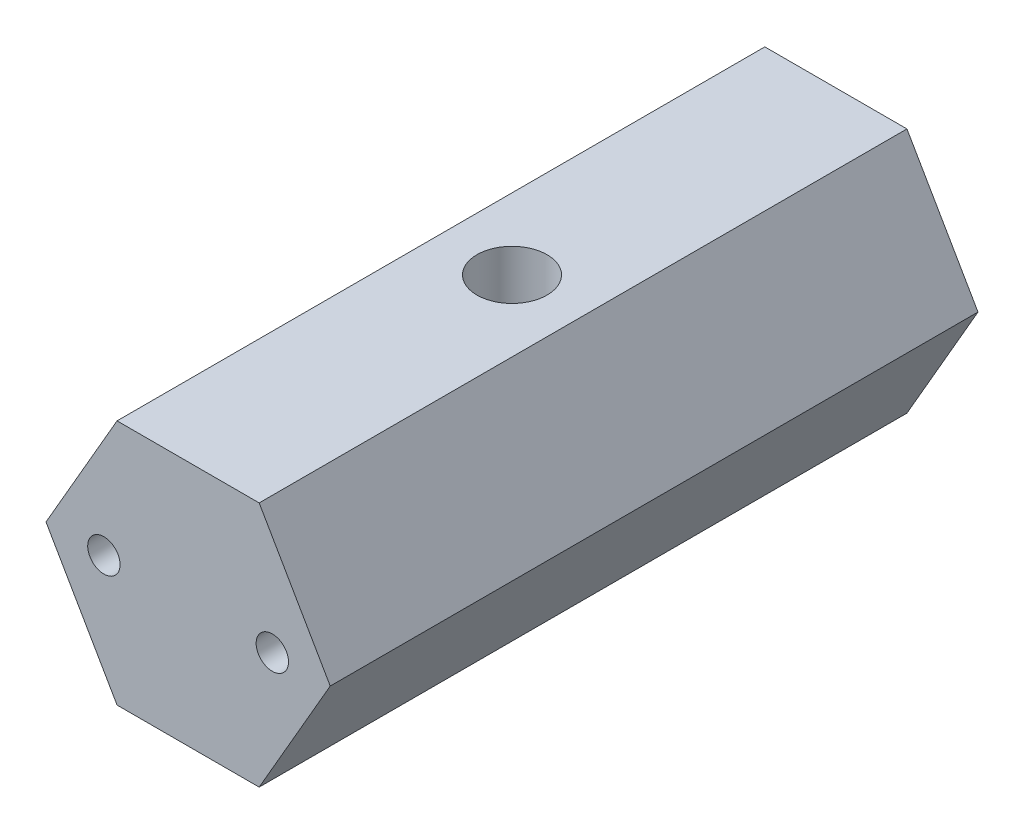
SolidWorks part; units mm, degrees
material "6061-T6 (SS)"
ref_plane "Front Plane" through (0, 0, 0) normal (0, 0, 1) x (1, 0, 0)
ref_plane "Top Plane" through (0, 0, 0) normal (0, 1, 0) x (1, 0, 0)
ref_plane "Right Plane" through (0, 0, 0) normal (1, 0, 0) x (0, 0, -1)
sketch "Sketch1" plane through (0, 0, 0) normal (0, 0, 1) x (1, 0, 0)
  line L1 (-5.4848, -9.5) -> (5.4848, -9.5)
  line L2 (5.4848, -9.5) -> (10.9697, 0)
  line L3 (10.9697, 0) -> (5.4848, 9.5)
  line L4 (5.4848, 9.5) -> (-5.4848, 9.5)
  line L5 (-5.4848, 9.5) -> (-10.9697, 0)
  line L6 (-10.9697, 0) -> (-5.4848, -9.5)
  circle A0 centre (0, 0) radius 9.5 construction
  circle A1 centre (-6.5, 0) radius 1.25
  circle A2 centre (-6.5, 0) radius 1.5 construction
  circle A3 centre (6.5, 0) radius 1.25
  circle A4 centre (6.5, 0) radius 1.5 construction
  point P20 (0, 0)
  dimension "D1" = 2.5
  dimension "D2" = 3
  dimension "D3" = 2
  dimension "D4" = 19
  dimension "D5" = 13
extrude "Boss-Extrude1" add sketch "Sketch1" along normal mid plane 50
hole_wizard "1/4-28 Tapped Hole1" positions "Sketch2" profile "Sketch3" tap size "1/4-28" standard "ANSI Inch" end condition up to next
sketch "Sketch2" plane through (0, 9.5, 0) normal (0, 1, 0) x (1, 0, 0)
  point P0 (0, 0)
cosmetic thread "Hole Thread1" parameters "D2"=6.35
sketch "Sketch3" plane through (0, 9.5, 0) normal (1, 0, 0) x (0, 0, 1)
  line L0 (0, 0) -> (0, 19)
  line L1 (0, 19) -> (2.7051, 19)
  line L2 (2.7051, 19) -> (2.7051, 0)
  line L5 (2.7051, 0) -> (0, 0)
  line L11 (0, -6.35) -> (0, 107.95) construction
  dimension "Thru Tap Drill Dia." = 5.4102
  dimension "Thru Tap Drill Depth" = 19
